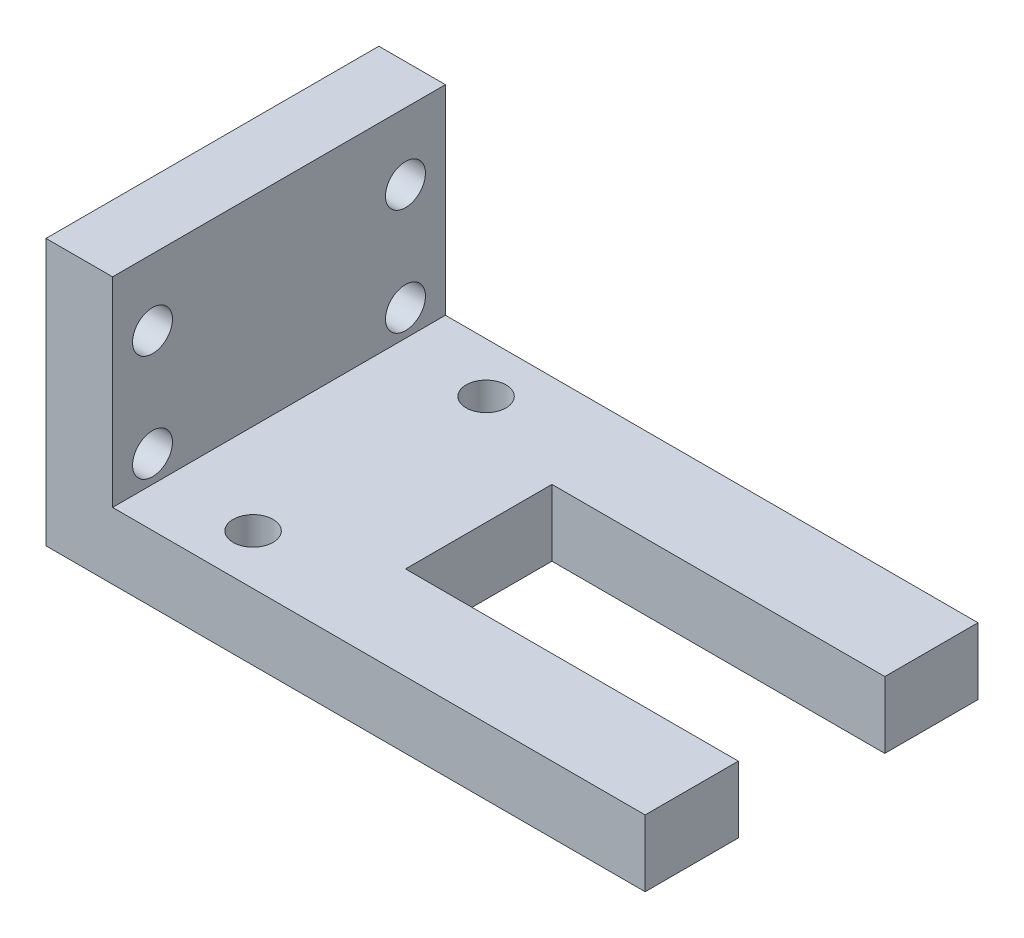
SolidWorks part; units mm, degrees
ref_plane "Front Plane" through (0, 0, 0) normal (0, 0, 1) x (1, 0, 0)
ref_plane "Top Plane" through (0, 0, 0) normal (0, 1, 0) x (1, 0, 0)
ref_plane "Right Plane" through (0, 0, 0) normal (1, 0, 0) x (0, 0, -1)
sketch "Sketch1" plane through (0, 0, 0) normal (0, 0, 1) x (1, 0, 0)
  line L0 (0, 27.931) -> (0, 12.931)
  line L1 (0, 12.931) -> (40, 12.931)
  line L2 (40, 12.931) -> (40, 7.931)
  line L3 (40, 7.931) -> (-5, 7.931)
  line L4 (-5, 7.931) -> (-5, 27.931)
  line L5 (-5, 27.931) -> (0, 27.931)
  dimension "D1" = 45
  dimension "D2" = 20
  dimension "D3" = 5
  dimension "D4" = 5
extrude "Boss-Extrude1" add sketch "Sketch1" against normal blind 25
sketch "Sketch2" plane through (-5, 0, 0) normal (-1, 0, 0) x (0, 0, 1)
  line L0 (-25, 7.931) -> (0, 7.931) construction
  line L1 (-12.5, 27.931) -> (-12.5, 7.931)
  line L2 (-25, 27.931) -> (0, 27.931) construction
  circle A0 centre (-22, 22.931) radius 1.5
  circle A1 centre (-3, 22.931) radius 1.5
  circle A2 centre (-22, 14.931) radius 1.5
  circle A3 centre (-3, 14.931) radius 1.5
  dimension "D1" = 3
  dimension "D2" = 15
  dimension "D3" = 15
  dimension "D4" = 7
  dimension "D5" = 7
  dimension "D6" = 9.5
  dimension "D7" = 9.5
  dimension "D8" = 9.5
  dimension "D9" = 9.5
extrude "Cut-Extrude1" cut sketch "Sketch2" against normal blind 26 contours A0 | A1 | A3 | A2
sketch "Sketch3" plane through (0, 7.931, 0) normal (0, -1, 0) x (1, 0, 0)
  line L0 (-5, 0) -> (40, 0) construction
  line L2 (40, -25) -> (40, 0) construction
  line L3 (40, -8) -> (15, -8)
  line L4 (40, -8) -> (40, -17)
  line L5 (40, -17) -> (15, -17)
  line L6 (15, -8) -> (15, -17)
  circle A0 centre (6.802, -3.75) radius 1.5
  circle A1 centre (6.802, -21.25) radius 1.5
  point P6 (0, 0)
  dimension "D2" = 3
  dimension "D3" = 3.75
  dimension "D1" = 17.5
  dimension "D4" = 25
  dimension "D5" = 9
  dimension "D6" = 8
extrude "Cut-Extrude2" cut sketch "Sketch3" against normal blind 10
sketch "Sketch5" plane through (0, 7.931, 0) normal (0, -1, 0) x (1, 0, 0)
  line L0 (40, -8) -> (40, 0) construction
  line L1 (15, -8) -> (40, -8)
  line L2 (15, -8) -> (15, -7)
  line L3 (15, -7) -> (40, -7)
  line L4 (40, -8) -> (40, -7)
  line L5 (40, -25) -> (40, -17) construction
  line L6 (15, -17) -> (40, -17)
  line L7 (15, -17) -> (15, -18)
  line L8 (15, -18) -> (40, -18)
  line L9 (40, -17) -> (40, -18)
  dimension "D1" = 1
  dimension "D2" = 1
extrude "Cut-Extrude3" cut sketch "Sketch5" against normal blind 50
